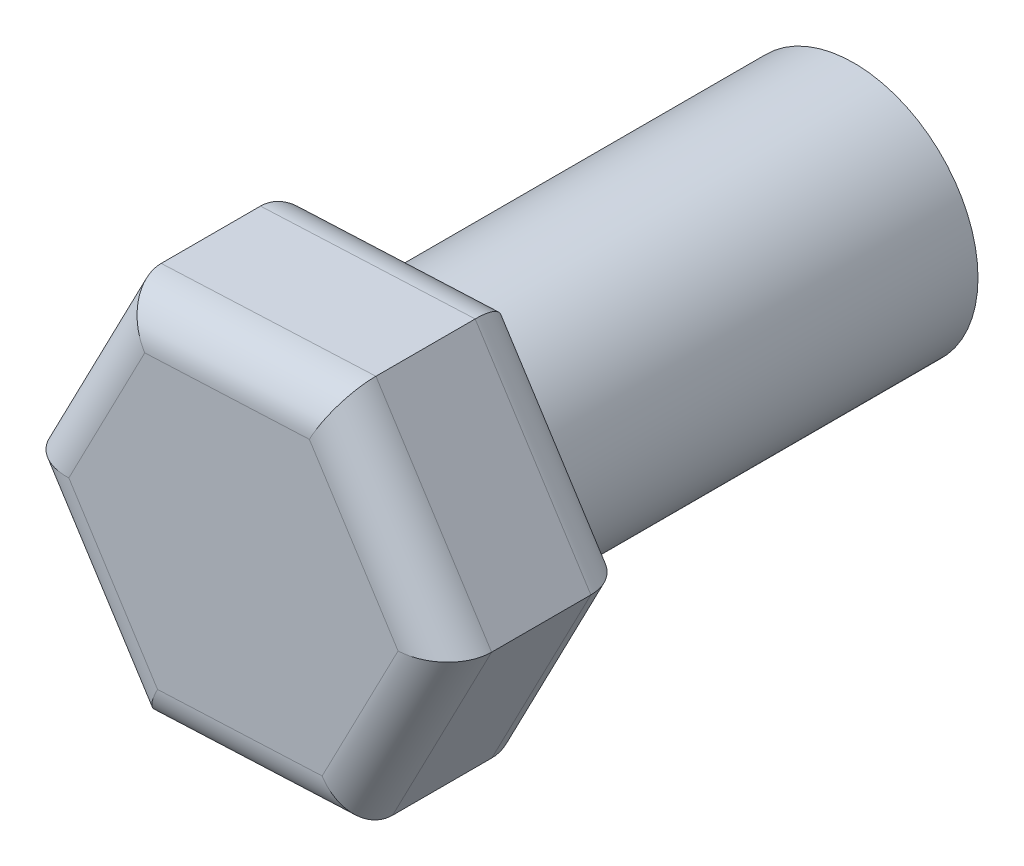
SolidWorks part; units mm, degrees
ref_plane "Front Plane" through (0, 0, 0) normal (0, 0, 1) x (1, 0, 0)
ref_plane "Top Plane" through (0, 0, 0) normal (0, 1, 0) x (1, 0, 0)
ref_plane "Right Plane" through (0, 0, 0) normal (1, 0, 0) x (0, 0, -1)
sketch "Sketch1" plane through (0, 0, 0) normal (0, 0, 1) x (1, 0, 0)
  circle A0 centre (0, 0) radius 2
extrude "Boss-Extrude1" add sketch "Sketch1" along normal blind 7
sketch "Sketch2" plane through (0, 0, 7) normal (0, 0, 1) x (1, 0, 0)
  line L0 (-1.5959, -3.0746) -> (1.8647, -2.9194)
  line L1 (1.5959, 3.0746) -> (-1.8647, 2.9194)
  line L2 (-1.8647, 2.9194) -> (-3.4606, -0.1552)
  line L3 (-3.4606, -0.1552) -> (-1.5959, -3.0746)
  line L4 (1.8647, -2.9194) -> (3.4606, 0.1552)
  line L5 (3.4606, 0.1552) -> (1.5959, 3.0746)
  circle A0 centre (0, 0) radius 3 construction
extrude "Boss-Extrude2" add sketch "Sketch2" along normal blind 3
fillet "Fillet1" radius 0.7 12 edges at (-2.5283, -1.6149, 10) (-2.6627, 1.3821, 10) (-0.1344, 2.997, 10) (2.5283, 1.6149, 10) (2.6627, -1.3821, 10) (0.1344, -2.997, 10) (-0.1344, 2.997, 7) (-2.6627, 1.3821, 7) (-2.5283, -1.6149, 7) (0.1344, -2.997, 7) (2.6627, -1.3821, 7) (2.5283, 1.6149, 7)
